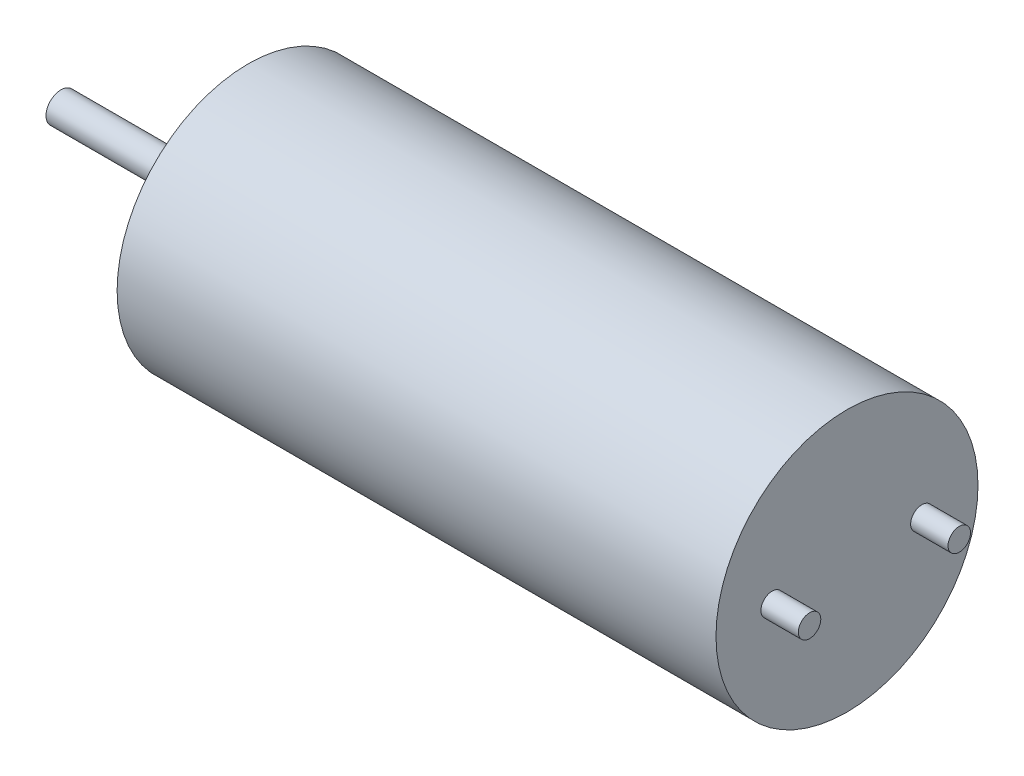
SolidWorks part; units mm, degrees
ref_plane "Front Plane" through (0, 0, 0) normal (0, 0, 1) x (1, 0, 0)
ref_plane "Top Plane" through (0, 0, 0) normal (0, 1, 0) x (1, 0, 0)
ref_plane "Right Plane" through (0, 0, 0) normal (1, 0, 0) x (0, 0, -1)
sketch "Sketch1" plane through (0, 0, 0) normal (1, 0, 0) x (0, 0, -1)
  circle A0 centre (0, 0) radius 3.5
  dimension "D1" = 7
extrude "Boss-Extrude1" add sketch "Sketch1" along normal blind 16
sketch "Sketch2" plane through (0, 0, 0) normal (-1, 0, 0) x (0, 0, 1)
  circle A0 centre (0, 0) radius 1.2
  dimension "D1" = 2.4
extrude "Boss-Extrude2" add sketch "Sketch2" along normal blind 0.8
sketch "Sketch3" plane through (-0.8, 0, 0) normal (-1, 0, 0) x (0, 0, 1)
  circle A0 centre (0, 0) radius 0.4
  dimension "D1" = 0.8
extrude "Boss-Extrude3" add sketch "Sketch3" along normal blind 4.2
sketch "Sketch4" plane through (16, 0, 0) normal (1, 0, 0) x (0, 0, -1)
  line L0 (-2, 0) -> (2, 0) construction
  circle A0 centre (-2, 0) radius 0.3
  circle A1 centre (2, 0) radius 0.3
  point P4 (0, 0)
  dimension "D2" = 0.6
  dimension "D1" = 4
extrude "Boss-Extrude4" add sketch "Sketch4" along normal blind 1
